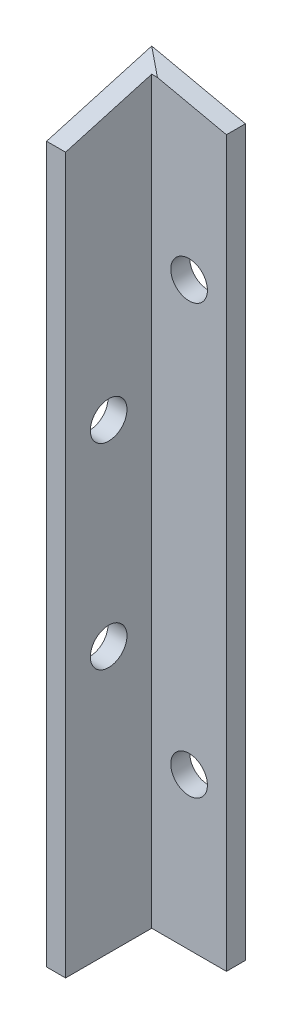
SolidWorks part; units mm, degrees
ref_plane "Front Plane" through (0, 0, 0) normal (0, 0, 1) x (1, 0, 0)
ref_plane "Top Plane" through (0, 0, 0) normal (0, 1, 0) x (1, 0, 0)
ref_plane "Right Plane" through (0, 0, 0) normal (1, 0, 0) x (0, 0, -1)
sketch "Sketch1" plane through (0, 0, 0) normal (0, 1, 0) x (1, 0, 0)
  line L0 (0, 0) -> (0, 13.85)
  line L1 (0, 13.85) -> (12.34, 13.85)
  line L2 (0, 0) -> (2.5, 0)
  line L3 (2.5, 0) -> (2.5, 11.35)
  line L4 (2.5, 11.35) -> (12.34, 11.35)
  line L5 (12.34, 11.35) -> (12.34, 13.85)
  dimension "D1" = 12.34
  dimension "D2" = 13.85
  dimension "D3" = 2.5
  dimension "D4" = 2.5
extrude "Boss-Extrude1" add sketch "Sketch1" along normal blind 100
sketch "Sketch4" plane through (0, 0, 0) normal (-1, 0, 0) x (0, 0, 1)
  line L3 (-13.85, 98.1575) -> (8.2643, 91.8664)
  line L4 (8.2643, 91.8664) -> (8.2643, 98.1575)
  line L5 (8.2643, 98.1575) -> (-13.85, 98.1575)
sketch "Sketch5" plane through (0, 0, -13.85) normal (0, 0, -1) x (-1, 0, 0)
  line L3 (0, 98.1575) -> (-15.025, 99.3997)
  line L4 (-15.025, 99.3997) -> (-15.025, 94.8678)
  line L5 (0, 98.1575) -> (-15.025, 94.8678)
  line L6 (0, 100) -> (0, 0) construction
extrude "Cut-Extrude5" cut sketch "Sketch5" against normal blind 16 contours L4 L5 L3
extrude "Cut-Extrude6" cut sketch "Sketch4" against normal blind 16
sketch "Sketch6" plane through (0, 0, -11.35) normal (0, 0, 1) x (1, 0, 0)
  line L0 (2.5, 0) -> (12.34, 0) construction
  line L1 (3.2482, 97.4463) -> (12.34, 95.4557) construction
  circle A0 centre (7.42, 20) radius 2.415
  circle A1 centre (7.42, 76.451) radius 2.415
  point P8 (7.7941, 96.451)
  dimension "D3" = 4.83
  dimension "D4" = 4.83
  dimension "D1" = 20
  dimension "D2" = 20
sketch "Sketch8" plane through (2.5, 0, 0) normal (1, 0, 0) x (0, 0, -1)
  line L0 (0, 0) -> (11.35, 0) construction
  line L1 (11.35, 97.4463) -> (0, 94.2175) construction
  circle A0 centre (5.675, 35) radius 2.415
  circle A1 centre (5.675, 60.8319) radius 2.415
  point P8 (5.675, 95.8319)
  dimension "D3" = 4.83
  dimension "D4" = 4.83
  dimension "D1" = 35
  dimension "D2" = 35
extrude "Cut-Extrude7" cut sketch "Sketch8" against normal blind 16
extrude "Cut-Extrude8" cut sketch "Sketch6" against normal blind 16
